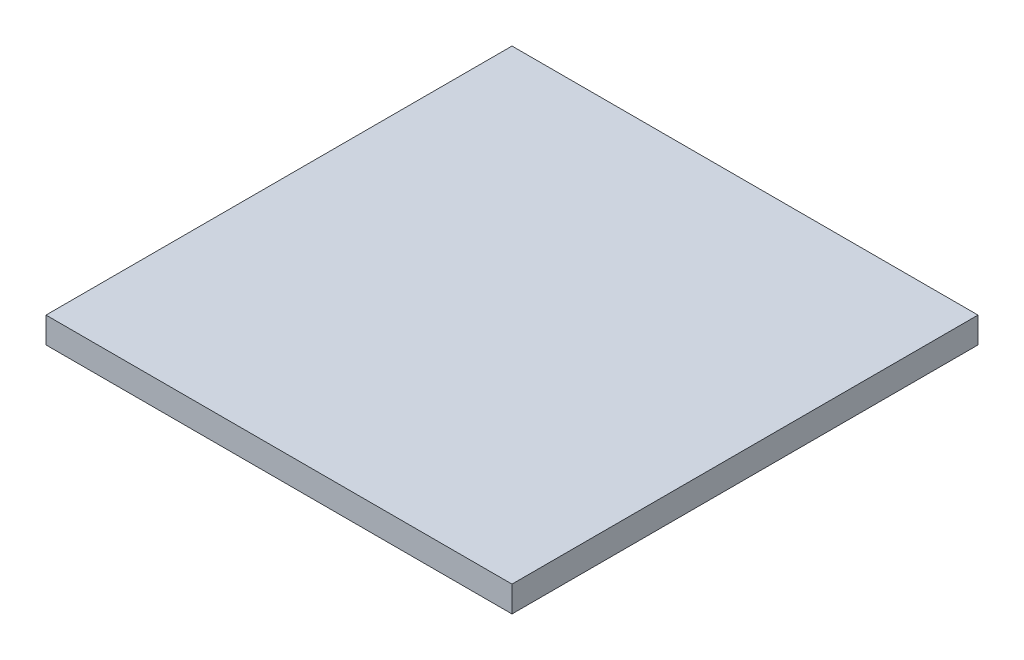
SolidWorks part; units mm, degrees
material "Glas"
ref_plane "Vorne" through (0, 0, 0) normal (0, 0, 1) x (1, 0, 0)
ref_plane "Oben" through (0, 0, 0) normal (0, 1, 0) x (1, 0, 0)
ref_plane "Rechts" through (0, 0, 0) normal (1, 0, 0) x (0, 0, -1)
sketch "Skizze1" plane through (0, 0, 0) normal (0, 1, 0) x (1, 0, 0)
  line L0 (-3.15, 3.15) -> (3.15, -3.15) construction
  line L1 (-3.15, 3.15) -> (3.15, 3.15)
  line L2 (-3.15, 3.15) -> (-3.15, -3.15)
  line L3 (-3.15, -3.15) -> (3.15, -3.15)
  line L4 (3.15, 3.15) -> (3.15, -3.15)
extrude "Aufsatz-Linear austragen1" add sketch "Skizze1" along normal blind 0.35
